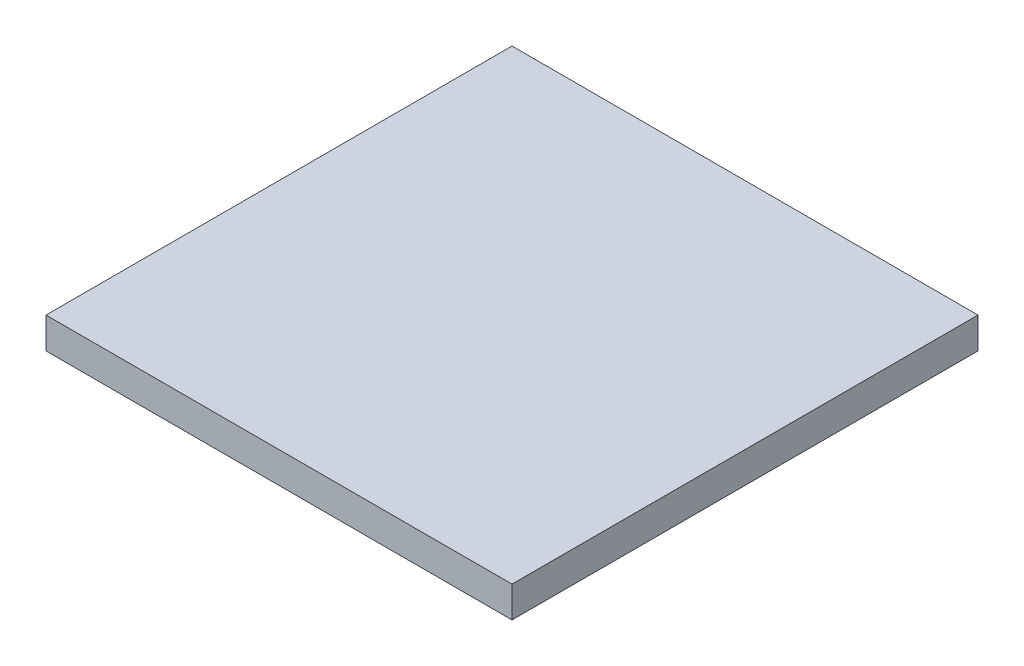
SolidWorks part; units mm, degrees
ref_plane "Front Plane" through (0, 0, 0) normal (0, 0, 1) x (1, 0, 0)
ref_plane "Top Plane" through (0, 0, 0) normal (0, 1, 0) x (1, 0, 0)
ref_plane "Right Plane" through (0, 0, 0) normal (1, 0, 0) x (0, 0, -1)
sketch "BaseS" plane through (0, 0, 0) normal (0, 1, 0) x (1, 0, 0)
  line L1 (-7.5, 7.5) -> (7.5, 7.5)
  line L2 (-7.5, 7.5) -> (-7.5, -7.5)
  line L3 (-7.5, -7.5) -> (7.5, -7.5)
  line L4 (7.5, 7.5) -> (7.5, -7.5)
  line L5 (-7.5, 7.5) -> (7.5, -7.5) construction
  line L6 (-7.5, -7.5) -> (7.5, 7.5) construction
  point P0 (0, 0)
  dimension "Dim" = 15
extrude "Base" add sketch "BaseS" along normal blind 1
